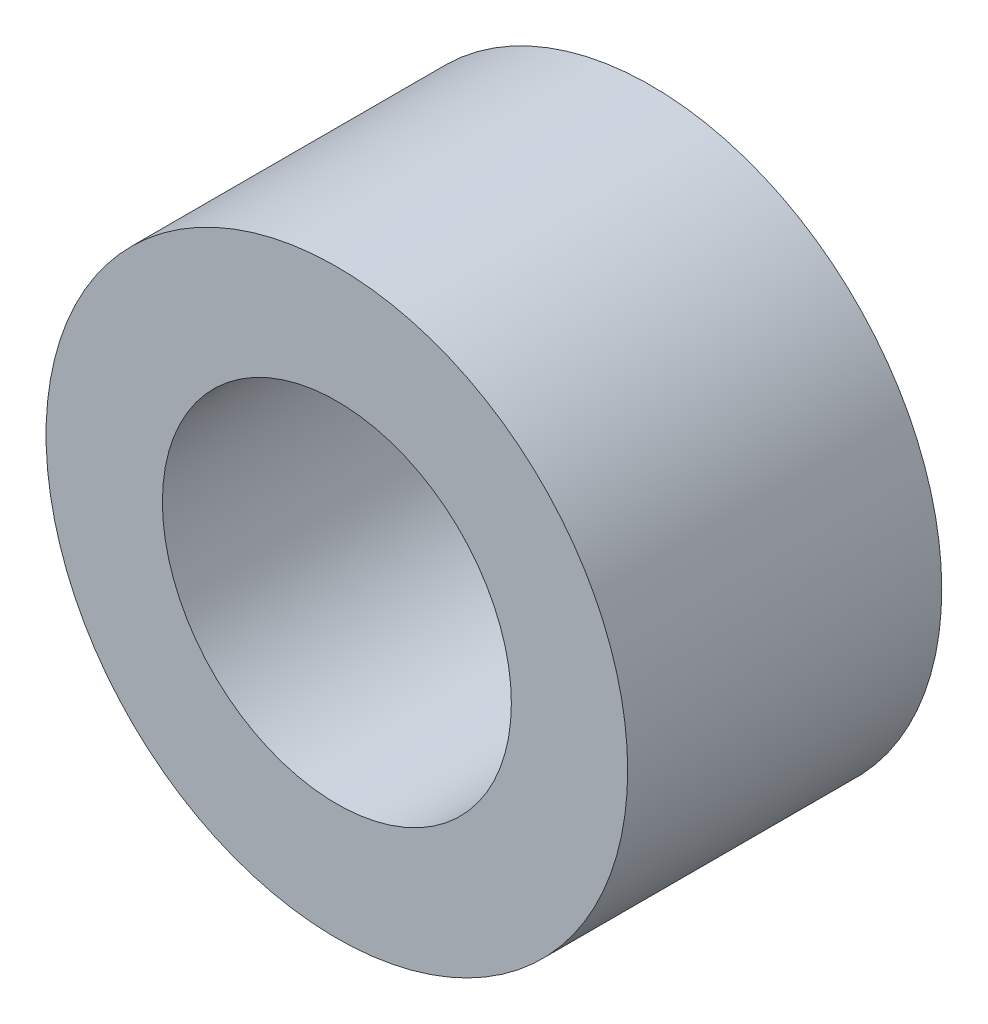
SolidWorks part; units mm, degrees
ref_plane "正面" through (0, 0, 0) normal (0, 0, 1) x (1, 0, 0)
ref_plane "平面" through (0, 0, 0) normal (0, 1, 0) x (1, 0, 0)
ref_plane "右側面" through (0, 0, 0) normal (1, 0, 0) x (0, 0, -1)
sketch "ｽｹｯﾁ1" plane through (0, 0, 0) normal (0, 0, 1) x (1, 0, 0)
  circle A0 centre (0, 0) radius 3
  circle A1 centre (0, 0) radius 5
  dimension "D1" = 6
  dimension "D2" = 10
extrude "ﾎﾞｽ - 押し出し1" add sketch "ｽｹｯﾁ1" along normal blind 5.4
